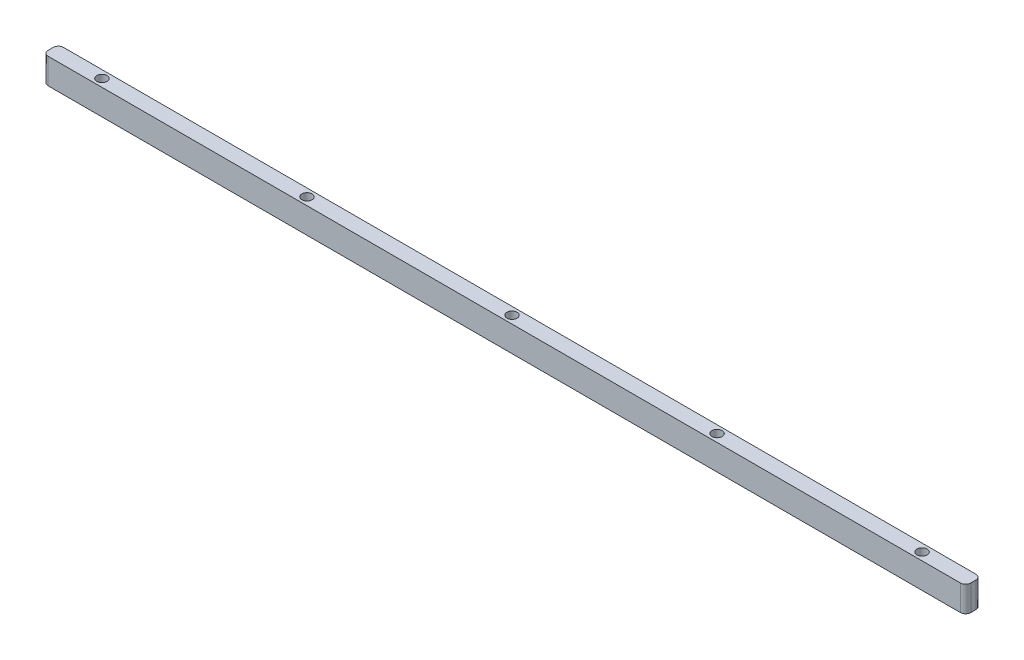
SolidWorks part; units mm, degrees
ref_plane "Front Plane" through (0, 0, 0) normal (0, 0, 1) x (1, 0, 0)
ref_plane "Top Plane" through (0, 0, 0) normal (0, 1, 0) x (1, 0, 0)
ref_plane "Right Plane" through (0, 0, 0) normal (1, 0, 0) x (0, 0, -1)
sketch "Sketch1" plane through (0, 0, 0) normal (0, 1, 0) x (1, 0, 0)
  line L1 (-90, -1.5) -> (90, -1.5)
  line L2 (-90, -1.5) -> (-90, 1.5)
  line L3 (-90, 1.5) -> (90, 1.5)
  line L4 (90, -1.5) -> (90, 1.5)
  line L5 (-90, -1.5) -> (90, 1.5) construction
  line L6 (-90, 1.5) -> (90, -1.5) construction
  circle A0 centre (0, 0) radius 1.5
  circle A1 centre (0, 0) radius 1
  circle A2 centre (40, 0) radius 1
  circle A3 centre (80, 0) radius 1
  circle A4 centre (-40, 0) radius 1
  circle A5 centre (-80, 0) radius 1
  point P0 (0, 0)
  dimension "D3" = 3
  dimension "D7" = 40
  dimension "D8" = 40
  dimension "D1" = 3
  dimension "D2" = 180
  dimension "D4" = 0.5
  dimension "D5" = 3
  dimension "D6" = 3
extrude "Boss-Extrude1" add sketch "Sketch1" along normal blind 5 contours A0 L3 L2 L1 A5 A4 | A0 L1 L4 L3 A3 A2 | A1
fillet "Fillet1" radius 1 4 edges at (90, 2.5, -1.5) (90, 2.5, 1.5) (-90, 2.5, -1.5) (-90, 2.5, 1.5)
